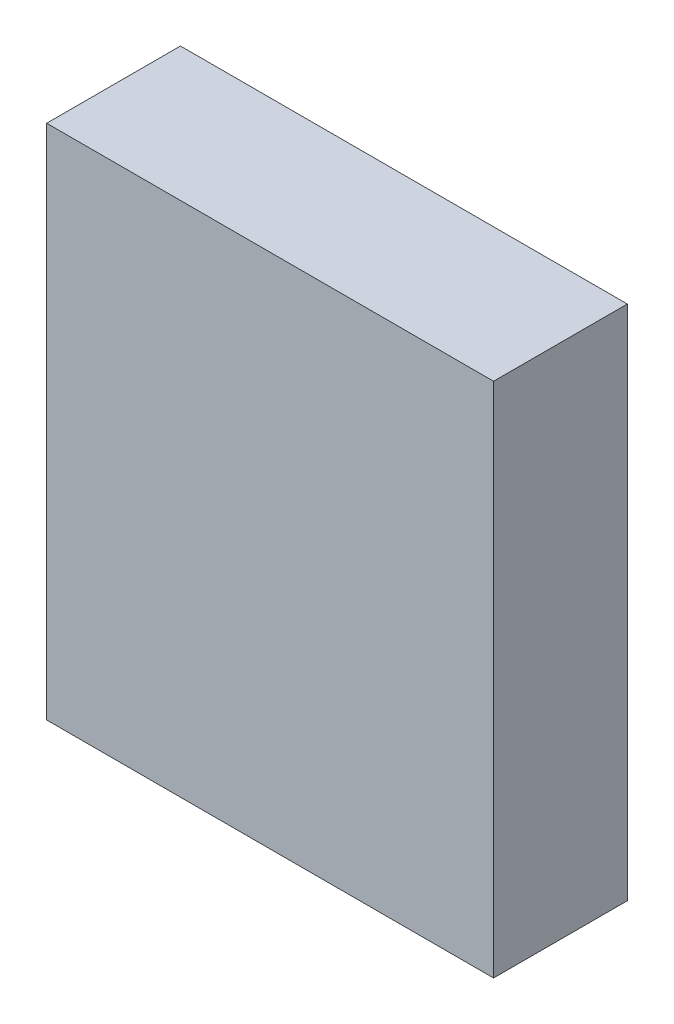
SolidWorks part; units mm, degrees
material "柚木"
ref_plane "前视基准面" through (0, 0, 0) normal (0, 0, 1) x (1, 0, 0)
ref_plane "上视基准面" through (0, 0, 0) normal (0, 1, 0) x (1, 0, 0)
ref_plane "右视基准面" through (0, 0, 0) normal (1, 0, 0) x (0, 0, -1)
sketch "草图1" plane through (0, 0, 0) normal (0, 1, 0) x (1, 0, 0)
  line L1 (0, 0) -> (-1470, 0)
  line L2 (0, 0) -> (0, 440)
  line L3 (0, 440) -> (-1470, 440)
  line L4 (-1470, 0) -> (-1470, 440)
  dimension "D1" = 440
  dimension "D2" = 1470
extrude "凸台-拉伸1" add sketch "草图1" along normal blind 1700
